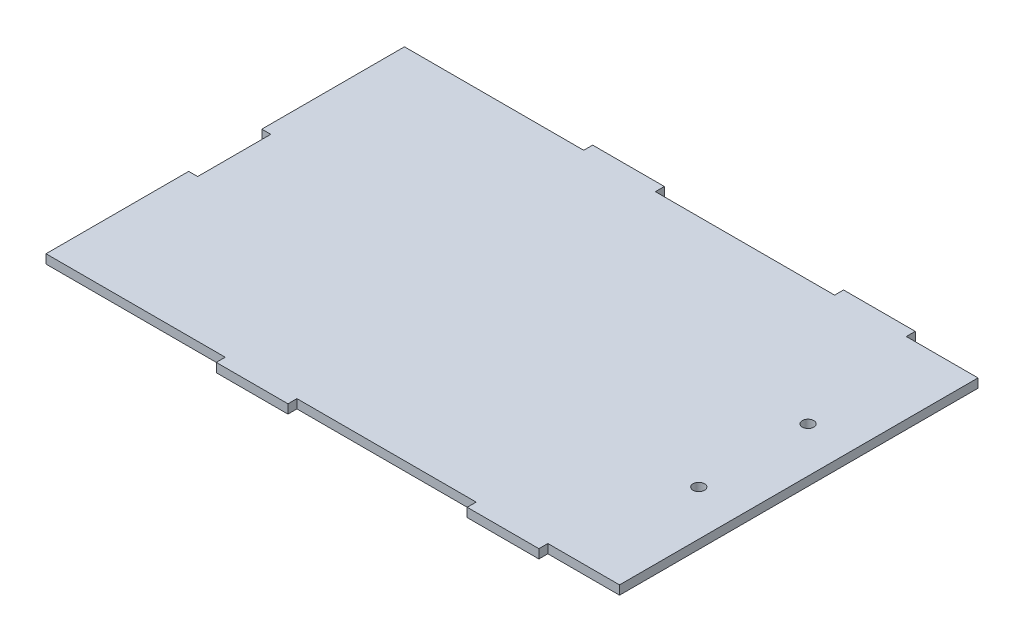
SolidWorks part; units mm, degrees
ref_plane "Front Plane" through (0, 0, 0) normal (0, 0, 1) x (1, 0, 0)
ref_plane "Top Plane" through (0, 0, 0) normal (0, 1, 0) x (1, 0, 0)
ref_plane "Right Plane" through (0, 0, 0) normal (1, 0, 0) x (0, 0, -1)
sketch "Sketch1" plane through (0, 0, 0) normal (0, 1, 0) x (1, 0, 0)
  line L0 (-59.2382, 11.4936) -> (143.9618, 11.4936) construction
  line L1 (-59.2382, 74.9936) -> (143.9618, 74.9936)
  line L2 (-59.2382, 74.9936) -> (-59.2382, -52.0064)
  line L3 (-59.2382, -52.0064) -> (143.9618, -52.0064)
  line L4 (143.9618, 74.9936) -> (143.9618, -52.0064)
  circle A0 centre (127.9598, -7.9374) radius 2.032
  circle A1 centre (127.9598, 30.7976) radius 2.032
  dimension "D3" = 4.064
  dimension "D4" = 4.064
  dimension "D1" = 127
  dimension "D2" = 203.2
extrude "Boss-Extrude1" add sketch "Sketch1" along normal blind 3.175
sketch "Sketch2" plane through (0, 3.175, 0) normal (0, 1, 0) x (1, 0, 0)
  line L0 (-59.2382, 11.4936) -> (143.9618, 11.4936) construction
  line L1 (-59.2382, 74.9936) -> (-59.2382, -52.0064) construction
  line L2 (143.9618, -52.0064) -> (143.9618, 74.9936) construction
sketch "Sketch4" plane through (0, 0, 0) normal (0, -1, 0) x (1, 0, 0)
  line L0 (-59.2382, -11.4936) -> (143.9618, -11.4936) construction
  line L1 (-59.2382, -74.9936) -> (-59.2382, 52.0064) construction
  line L2 (143.9618, 52.0064) -> (143.9618, -74.9936) construction
sketch "Sketch5" plane through (0, 0, 52.0064) normal (0, 0, 1) x (1, 0, 0)
  line L0 (-59.2382, 3.175) -> (143.9618, 3.175) construction
  line L1 (29.6618, 3.175) -> (4.2618, 3.175)
  line L2 (29.6618, 3.175) -> (29.6618, 0)
  line L3 (29.6618, 0) -> (4.2618, 0)
  line L4 (4.2618, 3.175) -> (4.2618, 0)
  line L5 (-59.2382, 0) -> (143.9618, 0) construction
  line L7 (93.1618, 3.175) -> (118.5618, 3.175)
  line L8 (93.1618, 3.175) -> (93.1618, 0)
  line L9 (93.1618, 0) -> (118.5618, 0)
  line L10 (118.5618, 3.175) -> (118.5618, 0)
  line L11 (-59.2382, 3.175) -> (-59.2382, 0) construction
  dimension "D1" = 63.5
  dimension "D2" = 25.4
  dimension "D3" = 25.4
  dimension "D4" = 63.5
extrude "Boss-Extrude2" add sketch "Sketch5" along normal blind 3.175
sketch "Sketch6" plane through (0, 0, -74.9936) normal (0, 0, -1) x (-1, 0, 0)
  line L0 (-143.9618, 3.175) -> (59.2382, 3.175) construction
  line L1 (-118.5618, 3.175) -> (-93.1618, 3.175)
  line L2 (-118.5618, 3.175) -> (-118.5618, 0)
  line L3 (-118.5618, 0) -> (-93.1618, 0)
  line L4 (-93.1618, 3.175) -> (-93.1618, 0)
  line L5 (-143.9618, 0) -> (59.2382, 0) construction
  line L7 (-29.6618, 3.175) -> (-4.2618, 3.175)
  line L8 (-29.6618, 3.175) -> (-29.6618, 0)
  line L9 (-29.6618, 0) -> (-4.2618, 0)
  line L10 (-4.2618, 3.175) -> (-4.2618, 0)
  point P15 (0, 0)
  point P16 (0, 0)
  point P18 (0, 0)
  dimension "D1" = 25.4
  dimension "D2" = 25.4
extrude "Boss-Extrude3" add sketch "Sketch6" along normal blind 3.175
sketch "Sketch7" plane through (-59.2382, 0, 0) normal (-1, 0, 0) x (0, 0, 1)
  line L0 (-74.9936, 3.175) -> (52.0064, 3.175) construction
  line L1 (1.4604, 3.175) -> (-24.4476, 3.175)
  line L2 (1.4604, 3.175) -> (1.4604, 0)
  line L3 (1.4604, 0) -> (-24.4476, 0)
  line L4 (-24.4476, 3.175) -> (-24.4476, 0)
  line L5 (-74.9936, 0) -> (52.0064, 0) construction
  line L6 (-74.9936, 3.175) -> (-74.9936, 0) construction
  dimension "D1" = 25.908
  dimension "D2" = 50.546
extrude "Cut-Extrude1" cut sketch "Sketch7" against normal blind 3.175
